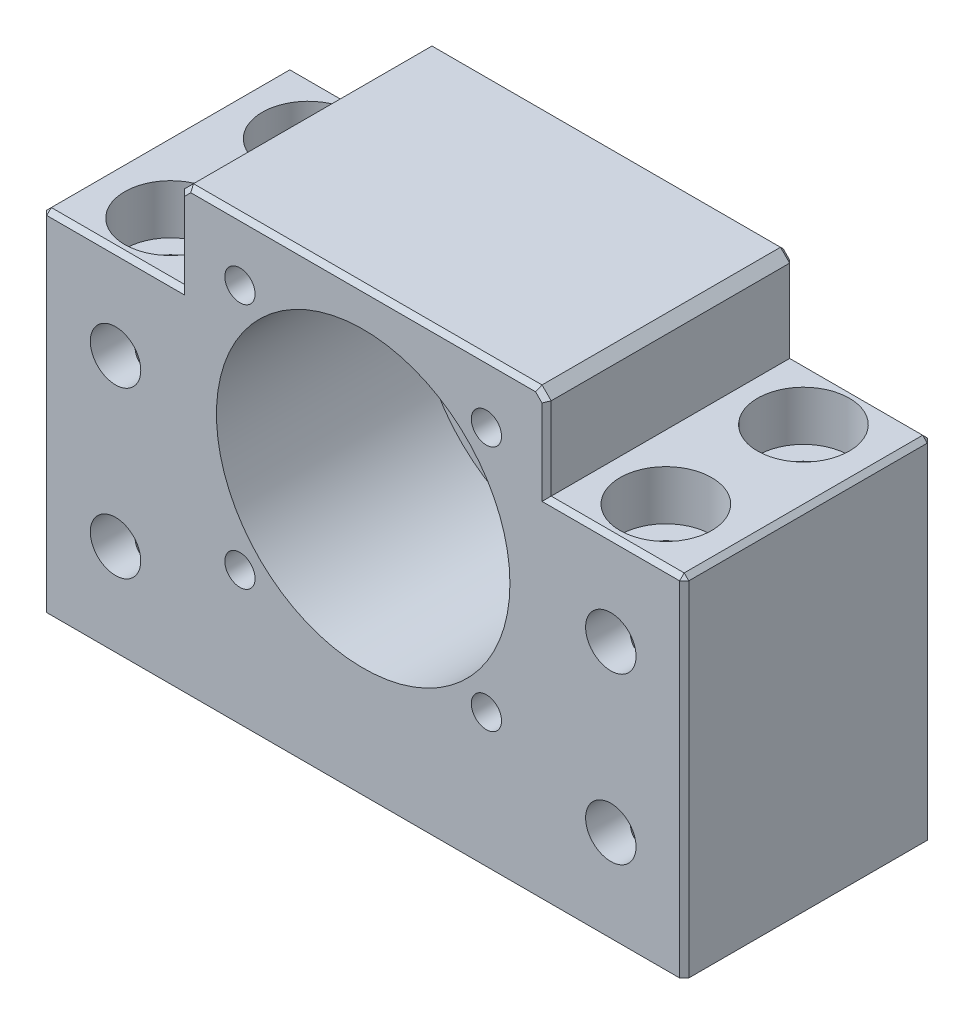
SolidWorks part; units mm, degrees
ref_plane "前基準面" through (0, 0, 0) normal (0, 0, 1) x (1, 0, 0)
ref_plane "上基準面" through (0, 0, 0) normal (0, 1, 0) x (1, 0, 0)
ref_plane "右基準面" through (0, 0, 0) normal (1, 0, 0) x (0, 0, -1)
sketch "草圖1" plane through (0, 0, 0) normal (0, 0, 1) x (1, 0, 0)
  line L0 (55, 38) -> (70, 38)
  line L1 (0, 0) -> (70, 0)
  line L2 (0, 0) -> (0, 38)
  line L3 (0, 38) -> (15, 38)
  line L4 (70, 0) -> (70, 38)
  line L6 (15, 38) -> (15, 48)
  line L7 (15, 48) -> (55, 48)
  line L8 (55, 38) -> (55, 48)
  circle A0 centre (35, 28) radius 14
  circle A1 centre (8, 28) radius 2.75
  circle A2 centre (62, 28) radius 2.75
  circle A3 centre (8, 10) radius 2.75
  circle A4 centre (62, 10) radius 2.75
  dimension "D4" = 28
  dimension "D7" = 5.5
  dimension "D8" = 5.5
  dimension "D9" = 5.5
  dimension "D10" = 5.5
  dimension "D1" = 70
  dimension "D2" = 38
  dimension "D3" = 48
  dimension "D5" = 35
  dimension "D6" = 28
  dimension "D11" = 54
  dimension "D12" = 8
  dimension "D13" = 40
  dimension "D14" = 15
  dimension "D15" = 18
extrude "填料-伸長1" add sketch "草圖1" against normal blind 27
chamfer "導角2" distance 1 angle 45 2 edges at (15, 48, -13.5) (55, 48, -13.5)
hole_wizard "M5 六角承窩頭蓋螺釘的柱孔4" positions "草圖9" profile "草圖11" counterbore size "M5" standard "ISO" end condition through all
sketch "草圖9" plane through (0, 38, 0) normal (0, 1, 0) x (1, 0, 0)
  point P0 (8, 21)
  point P2 (8, 6)
  point P4 (62, 21)
  point P6 (62, 6)
  dimension "D1" = 15
  dimension "D2" = 6
  dimension "D3" = 54
  dimension "D4" = 8
sketch "草圖11" plane through (8, 38, -21) normal (1, 0, 0) x (0, 0, 1)
  line L0 (0, 0) -> (0, 38)
  line L1 (0, 38) -> (2.75, 38)
  line L3 (2.75, 38) -> (2.75, 5.4)
  line L4 (2.75, 5.4) -> (5, 5.4)
  line L5 (5, 5.4) -> (5, 0)
  line L7 (5, 0) -> (0, 0)
  line L11 (0, -6.35) -> (0, 107.95) construction
  dimension "貫穿孔直徑" = 5.5
  dimension "貫穿孔深度" = 38
  dimension "柱孔直徑" = 10
  dimension "柱孔深度" = 5.4
sketch "草圖12" plane through (0, 0, 0) normal (0, 0, 1) x (1, 0, 0)
  line L0 (35, 28) -> (15.5544, 28) construction
  line L1 (35, 28) -> (19.2853, 43.7147) construction
  circle A0 centre (35, 28) radius 19 construction
  dimension "D1" = 45
hole_wizard "M4 螺紋孔1" positions "草圖13" profile "草圖14" tap size "M4" standard "ISO"
sketch "草圖13" plane through (0, 0, 0) normal (0, 0, 1) x (1, 0, 0)
  line L0 (35, 28) -> (19.2853, 43.7147) construction
  circle A0 centre (35, 28) radius 19 construction
  point P0 (21.565, 41.435)
sketch "草圖14" plane through (21.565, 41.435, 0) normal (1, 0, 0) x (0, -1, 0)
  line L0 (0, 0) -> (0, 12.9914)
  line L1 (0, 12.9914) -> (1.65, 12)
  line L2 (1.65, 12) -> (1.65, 0)
  line L5 (1.65, 0) -> (0, 0)
  line L10 (0, 12.9914) -> (-1.65, 12) construction
  line L11 (0, -6.35) -> (0, 107.95) construction
  dimension "螺孔鑽直徑" = 3.3
  dimension "螺孔鑽深度" = 12
  dimension "導頭角度" = 118
cosmetic thread "鑽孔螺紋1" parameters "D1"=10, "D2"=4
pattern_circular "環狀複製排列1" count 4 over 360 about axis through (35, 28, 0) along (0, 0, 1) of "M4 螺紋孔1"
sketch "草圖15" plane through (0, 0, 0) normal (0, 0, 1) x (1, 0, 0)
  circle A0 centre (35, 28) radius 16
  circle A1 centre (35, 28) radius 14
  dimension "D1" = 28
extrude "除料-伸長1" cut sketch "草圖15" against normal blind 22
chamfer "導角3" distance 0.5 angle 45 20 edges at (0, 19, -27) (7.5, 38, -27) (15, 42.5, -27) (15.5, 47.5, -27) (35, 48, -27) (54.5, 47.5, -27) (55, 42.5, -27) (70, 19, -27) (62.5, 38, -27) (70, 38, -13.5) (0, 38, -13.5) (0, 19, 0) (7.5, 38, 0) (15, 42.5, 0) (15.5, 47.5, 0) (35, 48, 0) (54.5, 47.5, 0) (55, 42.5, 0) (62.5, 38, 0) (70, 19, 0)
